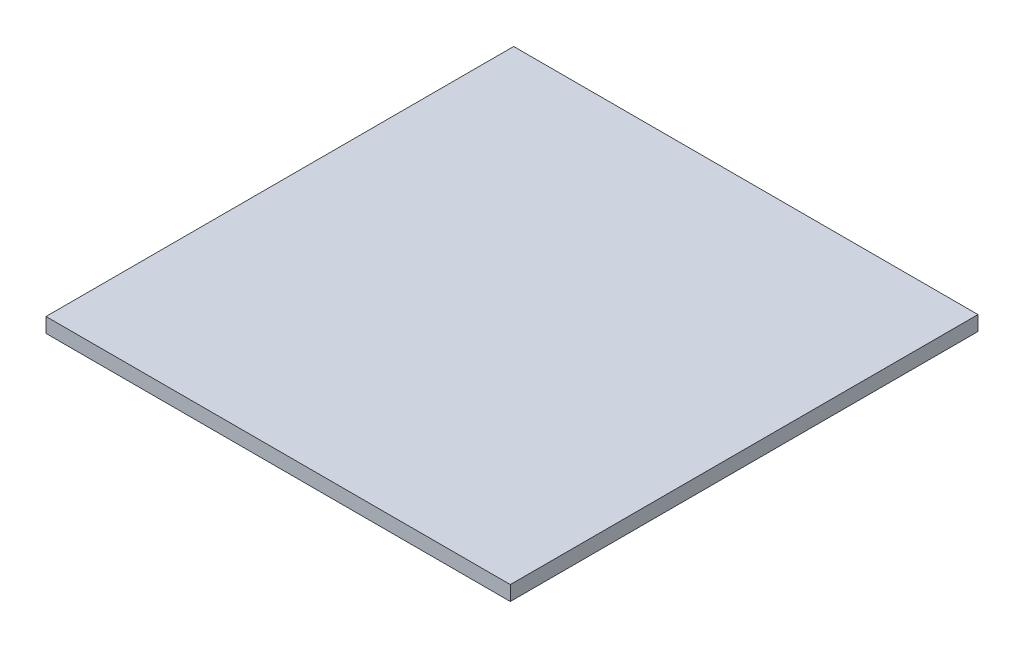
SolidWorks part; units mm, degrees
ref_plane "Front Plane" through (0, 0, 0) normal (0, 0, 1) x (1, 0, 0)
ref_plane "Top Plane" through (0, 0, 0) normal (0, 1, 0) x (1, 0, 0)
ref_plane "Right Plane" through (0, 0, 0) normal (1, 0, 0) x (0, 0, -1)
sketch "Sketch1" plane through (0, 0, 0) normal (0, 1, 0) x (1, 0, 0)
  line L1 (0, 0) -> (139, 0)
  line L2 (0, 0) -> (0, 140)
  line L3 (0, 140) -> (139, 140)
  line L4 (139, 0) -> (139, 140)
  dimension "D1" = 139
  dimension "D2" = 140
extrude "Boss-Extrude1" add sketch "Sketch1" along normal blind 4.4
